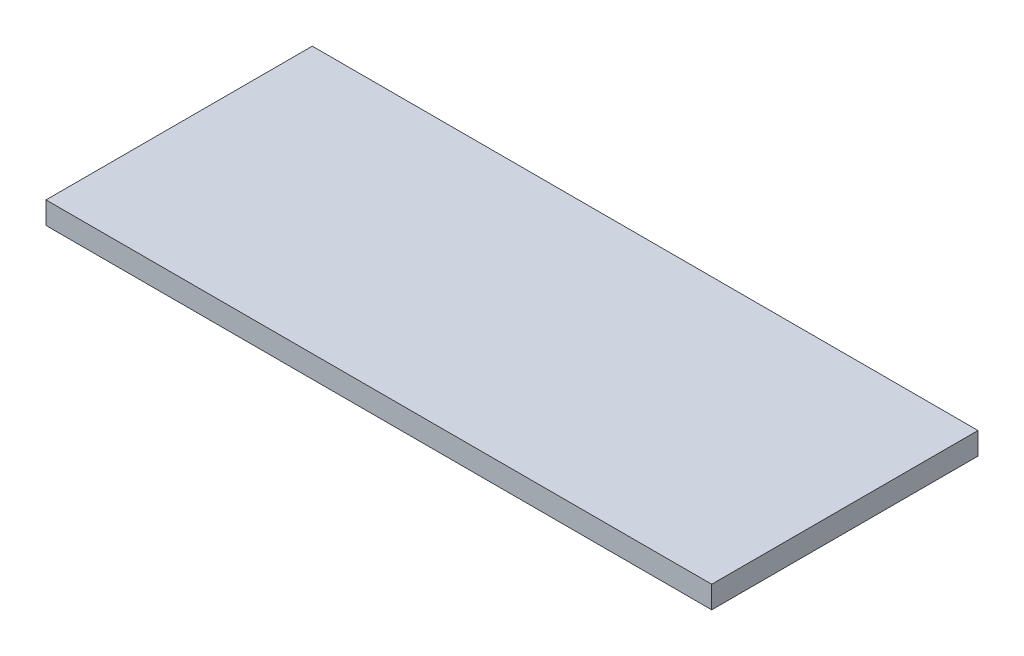
SolidWorks part; units mm, degrees
ref_plane "Płaszczyzna przednia" through (0, 0, 0) normal (0, 0, 1) x (1, 0, 0)
ref_plane "Płaszczyzna górna" through (0, 0, 0) normal (0, 1, 0) x (1, 0, 0)
ref_plane "Płaszczyzna prawa" through (0, 0, 0) normal (1, 0, 0) x (0, 0, -1)
sketch "Szkic1" plane through (0, 0, 0) normal (0, 1, 0) x (1, 0, 0)
  line L1 (-1500, -600) -> (1500, -600)
  line L2 (-1500, -600) -> (-1500, 600)
  line L3 (-1500, 600) -> (1500, 600)
  line L4 (1500, -600) -> (1500, 600)
  line L5 (-1500, -600) -> (1500, 600) construction
  line L6 (-1500, 600) -> (1500, -600) construction
  point P0 (0, 0)
  dimension "D1" = 1200
  dimension "D2" = 3000
extrude "Dodanie-wyciągnięcie1" add sketch "Szkic1" along normal blind 100
